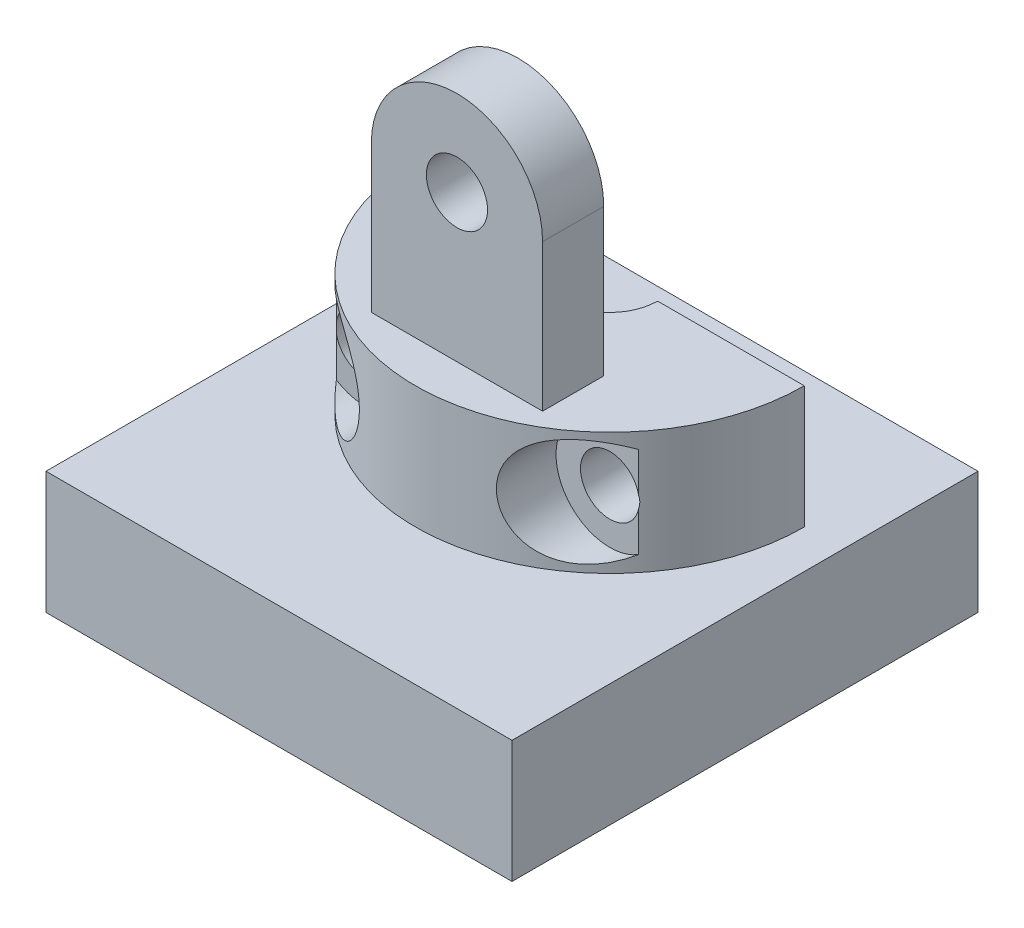
SolidWorks part; units mm, degrees
material "6061 Alloy"
ref_plane "Front Plane" through (0, 0, 0) normal (0, 0, 1) x (1, 0, 0)
ref_plane "Top Plane" through (0, 0, 0) normal (0, 1, 0) x (1, 0, 0)
ref_plane "Right Plane" through (0, 0, 0) normal (1, 0, 0) x (0, 0, -1)
sketch "Sketch1" plane through (0, 0, 0) normal (0, 1, 0) x (1, 0, 0)
  line L0 (1.95, 0) -> (7.9492, 0)
  line L1 (-1.95, 0) -> (-7.9492, 0)
  arc A0 (-7.9492, 0) -> (7.9492, 0) centre (0, 0) ccw
  arc A1 (1.95, 0) -> (-1.95, 0) centre (0, 0) cw
  dimension "D1" = 1.95
  dimension "D2" = 7.9492
extrude "Boss-Extrude1" add sketch "Sketch1" along normal mid plane 5 contours L0 A0 L1 A1
sketch "Sketch2" plane through (0, 2.5, 0) normal (0, 1, 0) x (1, 0, 0)
  line L0 (3.5, -3.75) -> (-3.5, -3.75)
  line L1 (-3.5, -3.75) -> (-3.5, -6.25)
  line L2 (3.5, -6.25) -> (3.5, -3.75)
  line L3 (3.5, -6.25) -> (-3.5, -6.25)
  line L4 (1.95, 0) -> (7.9492, 0) construction
  arc A0 (-1.95, 0) -> (1.95, 0) centre (0, 0) ccw construction
  dimension "D1" = 2.5
  dimension "D2" = 3.75
  dimension "D3" = 7
  dimension "D4" = 3.5
extrude "Boss-Extrude2" add sketch "Sketch2" along normal blind 9.5 contours L2 L0 L1 L3
sketch "Sketch3" plane through (0, 0, 3.75) normal (0, 0, -1) x (-1, 0, 0)
  line L0 (3.5, 12) -> (3.5, 2.5) construction
  line L1 (-3.5, 8.5) -> (-3.5, 14.8864)
  line L2 (-3.5, 14.8864) -> (0, 16.8092)
  line L3 (0, 16.8092) -> (3.5, 14.5)
  line L4 (3.5, 14.5) -> (3.5, 8.5)
  line L6 (-3.5, 12) -> (3.5, 12) construction
  line L7 (-3.5, 12) -> (-3.5, 2.5) construction
  arc A0 (3.5, 8.5) -> (-3.5, 8.5) centre (0, 8.5) ccw
extrude "Cut-Extrude1" cut sketch "Sketch3" against normal blind 9.5 contours L3 L4 A0 L1 L2
sketch "Sketch4" plane through (0, 0, 3.75) normal (0, 0, -1) x (-1, 0, 0)
  circle A0 centre (0, 8.5) radius 1.25
  dimension "D1" = 2.5
extrude "Cut-Extrude2" cut sketch "Sketch4" against normal blind 9.5
ref_plane "Plane1" through (0, 0, 7) normal (0, 0, -1) x (-1, 0, 0)
hole_wizard "CBORE for M2 SHCS1" positions "Sketch5" profile "Sketch7" counterbore size "M2" standard "ANSI Metric"
sketch "Sketch5" plane through (0, 0, 7) normal (0, 0, -1) x (-1, 0, 0)
  point P0 (-5, 0)
  point P2 (5, 0)
  dimension "D1" = 5
  dimension "D2" = 5
sketch "Sketch7" plane through (5, 0, 7) normal (1, 0, 0) x (0, -1, 0)
  line L0 (0, 0) -> (0, 7)
  line L1 (0, 7) -> (1.2, 7)
  line L3 (1.2, 7) -> (1.2, 2)
  line L4 (1.2, 2) -> (2.2, 2)
  line L5 (2.2, 2) -> (2.2, 0)
  line L7 (2.2, 0) -> (0, 0)
  line L11 (0, -6.35) -> (0, 107.95) construction
  dimension "Thru Hole Dia." = 2.4
  dimension "Thru Hole Depth" = 7
  dimension "C'Bore Dia." = 4.4
  dimension "C'Bore Depth" = 2
sketch "Sketch8" plane through (0, 0, 7) normal (0, 0, -1) x (-1, 0, 0)
  circle A0 centre (-5, 0) radius 2.2
  circle A1 centre (5, 0) radius 2.2
  arc A2 (-3.7669, 1.822) -> (-6.1798, 1.8569) centre (-5, 0) ccw construction
  arc A3 (3.7669, -1.822) -> (6.1798, -1.8569) centre (5, 0) ccw construction
extrude "Cut-Extrude3" cut sketch "Sketch8" against normal blind 9.5
sketch "Sketch9" plane through (0, 0, 0) normal (0, 0, 1) x (1, 0, 0)
  line L0 (0, 0.5) -> (-3, 2.5)
  line L1 (-1.95, 2.5) -> (-7.9492, 2.5) construction
  line L2 (-3, 2.5) -> (0, 2.5)
  line L3 (0, 2.5) -> (0, 0.5)
  dimension "D1" = 3
  dimension "D2" = 2
sketch "Sketch10" plane through (0, 0, 0) normal (0, 0, -1) x (-1, 0, 0)
  line L0 (1.95, -2.5) -> (-1.95, -2.5)
sketch "Sketch11" plane through (0, -2.5, 0) normal (0, -1, 0) x (1, 0, 0)
  line L0 (-1.95, 0) -> (-7.9492, 0) construction
  line L1 (9.525, 13.525) -> (-9.525, 13.525)
  line L2 (9.525, 13.525) -> (9.525, -5.525)
  line L3 (9.525, -5.525) -> (-9.525, -5.525)
  line L4 (-9.525, 13.525) -> (-9.525, -5.525)
  line L5 (9.525, 13.525) -> (-9.525, -5.525) construction
  line L6 (9.525, -5.525) -> (-9.525, 13.525) construction
  point P0 (0, 4)
  dimension "D1" = 19.05
  dimension "D2" = 19.05
  dimension "D3" = 4
extrude "Boss-Extrude3" add sketch "Sketch11" along normal blind 5
fillet "Fillet1" radius 0.07 2 edges at (-1.95, 0, 0) (1.95, 0, 0)
fillet "Fillet2" [suppressed] radius 0.07
sketch "Sketch12" plane through (0, -2.5, 0) normal (0, 1, 0) x (1, 0, 0)
  line L0 (-7.9492, 0) -> (7.9492, 0)
  arc A0 (-7.9492, 0) -> (7.9492, 0) centre (0, 0) ccw construction
  arc A1 (-7.9492, 0) -> (7.9492, 0) centre (0, 0) ccw
